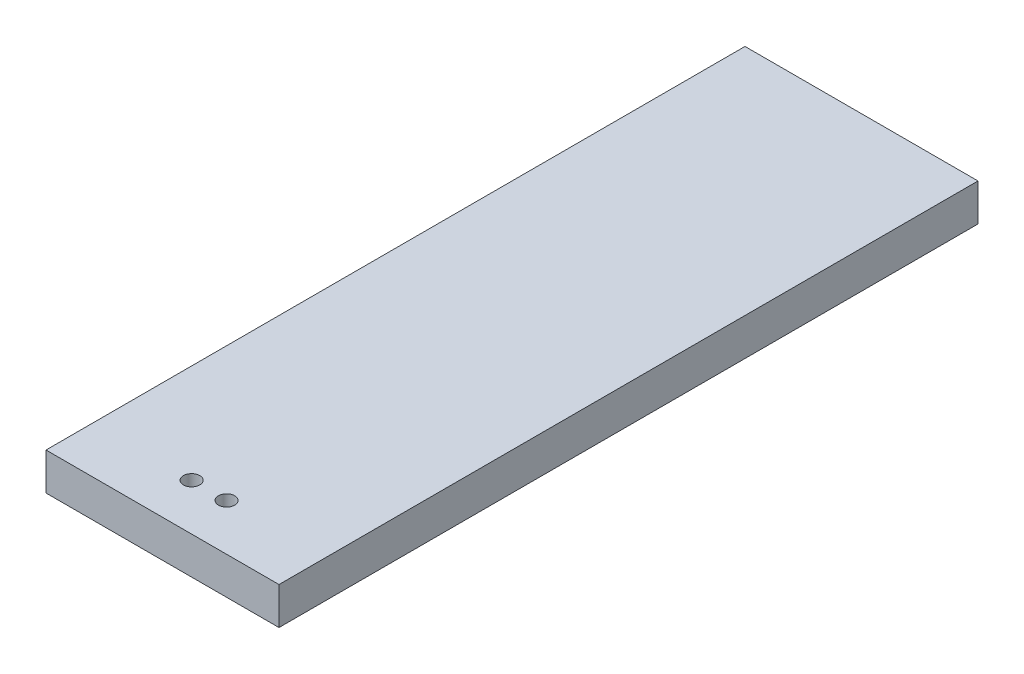
SolidWorks part; units mm, degrees
ref_plane "Front Plane" through (0, 0, 0) normal (0, 0, 1) x (1, 0, 0)
ref_plane "Top Plane" through (0, 0, 0) normal (0, 1, 0) x (1, 0, 0)
ref_plane "Right Plane" through (0, 0, 0) normal (1, 0, 0) x (0, 0, -1)
sketch "Sketch1" plane through (0, 0, 0) normal (0, 1, 0) x (1, 0, 0)
  line L1 (0, 0) -> (10, 0)
  line L2 (0, 0) -> (0, 30)
  line L3 (0, 30) -> (10, 30)
  line L4 (10, 0) -> (10, 30)
  dimension "D1" = 30
  dimension "D2" = 10
extrude "Boss-Extrude1" add sketch "Sketch1" along normal blind 1.6
sketch "Sketch2" plane through (0, 1.6, 0) normal (0, 1, 0) x (1, 0, 0)
  line L0 (10, 30) -> (0, 30) construction
  line L2 (3.5, 29.5) -> (3.5, 0)
  line L4 (6.5, 14.75) -> (6.5, 0)
  line L5 (0, 0) -> (10, 0) construction
  line L7 (5, 0) -> (5, 29.5)
  line L8 (5, 29.5) -> (3.5, 29.5)
  line L52 (3.5, 30.25) -> (6.5, 30.25)
  line L53 (3.5, 0) -> (6.5, 0)
  line L54 (3.5, 29.5) -> (3.5, 30.25)
  line L55 (6.5, 14.75) -> (6.5, 30.25)
  point P8 (5.0274, 28.9477)
  point P9 (0, 0)
  point P12 (10.6186, 0)
  point P13 (3.5, 30)
  point P14 (5, 0)
  point P16 (0, 0)
  point P17 (6.5, 17.8367)
  point P18 (0, 0)
  point P19 (5, 14.75)
  point P20 (5, 30)
  dimension "D1" = 0.5
  dimension "D2" = 3
  dimension "D3" = 0.25
sketch "Sketch3" plane through (0, 1.6, 0) normal (0, 1, 0) x (1, 0, 0)
  line L0 (4.25, 2) -> (5.75, 2) construction
  line L2 (5, 29.5) -> (3.5, 29.5) construction
  line L3 (5, 0) -> (5, 29.5) construction
  line L4 (4.25, 29.5) -> (4.25, 2) construction
  line L5 (0, 0) -> (10, 0) construction
  circle A0 centre (4.25, 2) radius 0.35
  circle A1 centre (5.75, 2) radius 0.35
  point P8 (4.25, 29.5)
  point P9 (5, 2)
  dimension "D1" = 0.7
  dimension "D2" = 2
extrude "Cut-Extrude1" cut sketch "Sketch3" against normal through all
